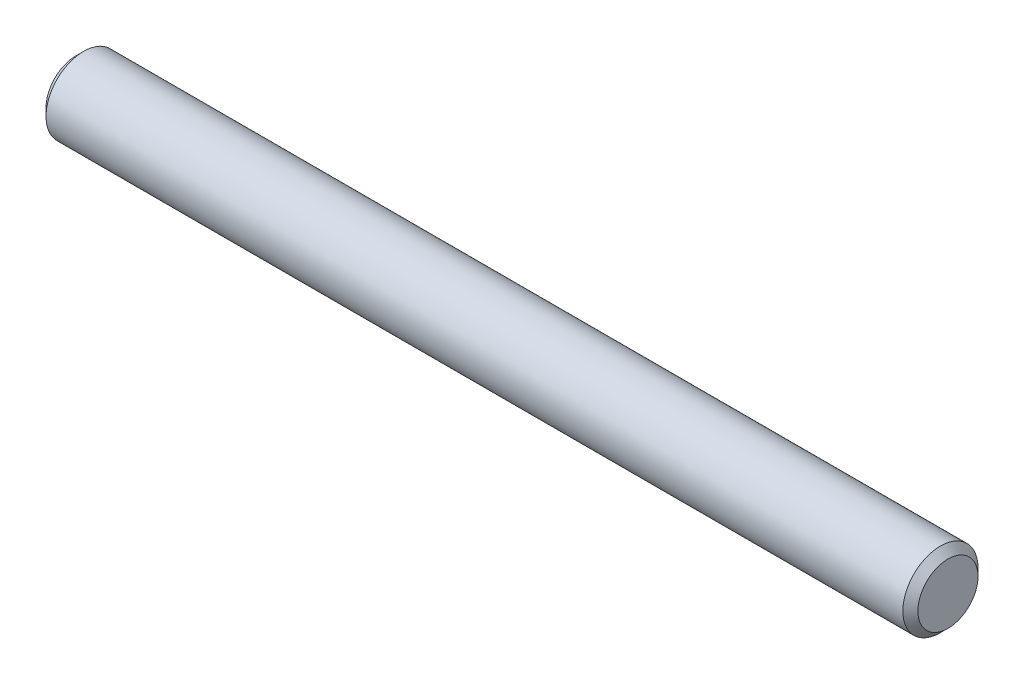
SolidWorks part; units mm, degrees
ref_plane "Front Plane" through (0, 0, 0) normal (0, 0, 1) x (1, 0, 0)
ref_plane "Top Plane" through (0, 0, 0) normal (0, 1, 0) x (1, 0, 0)
ref_plane "Right Plane" through (0, 0, 0) normal (1, 0, 0) x (0, 0, -1)
sketch "Sketch1" plane through (0, 0, 0) normal (1, 0, 0) x (0, 0, -1)
  circle A0 centre (0, 0) radius 5
  dimension "D1" = 10
extrude "Extrude1" add sketch "Sketch1" along normal blind 116
chamfer "Chamfer1" distance 1 angle 45 2 edges at (116, 0, -5) (0, 0, -5)
